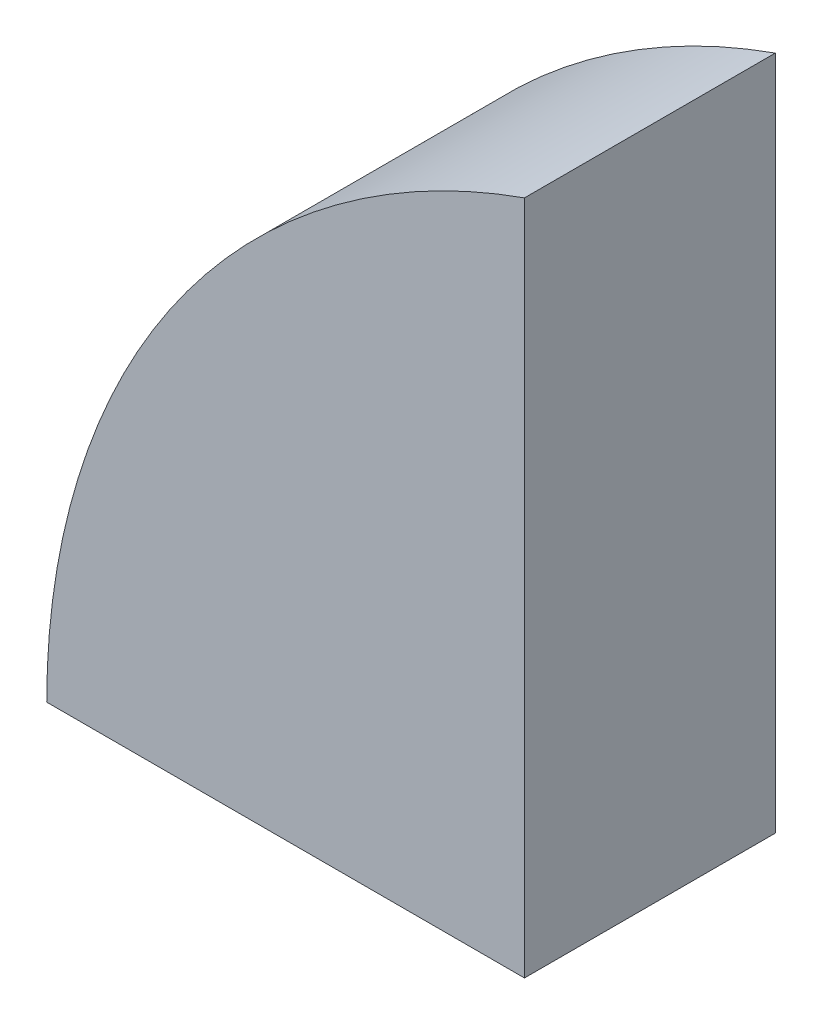
SolidWorks part; units mm, degrees
ref_plane "Plan de face" through (0, 0, 0) normal (0, 0, 1) x (1, 0, 0)
ref_plane "Plan de dessus" through (0, 0, 0) normal (0, 1, 0) x (1, 0, 0)
ref_plane "Plan de droite" through (0, 0, 0) normal (1, 0, 0) x (0, 0, -1)
sketch "Esquisse2" plane through (0, 0, 0) normal (0, 0, 1) x (1, 0, 0)
  line L0 (-124.883, -169.1228) -> (8.4503, -169.1228)
  line L2 (8.4503, -169.1228) -> (8.4503, 19.439)
  arc A0 (8.4503, 19.439) -> (-124.883, -169.1228) centre (75.117, -169.1228) ccw
  point P5 (8.4503, -169.1228)
  dimension "D3" = 133.3333
extrude "Boss.-Extru.2" add sketch "Esquisse2" along normal blind 70
